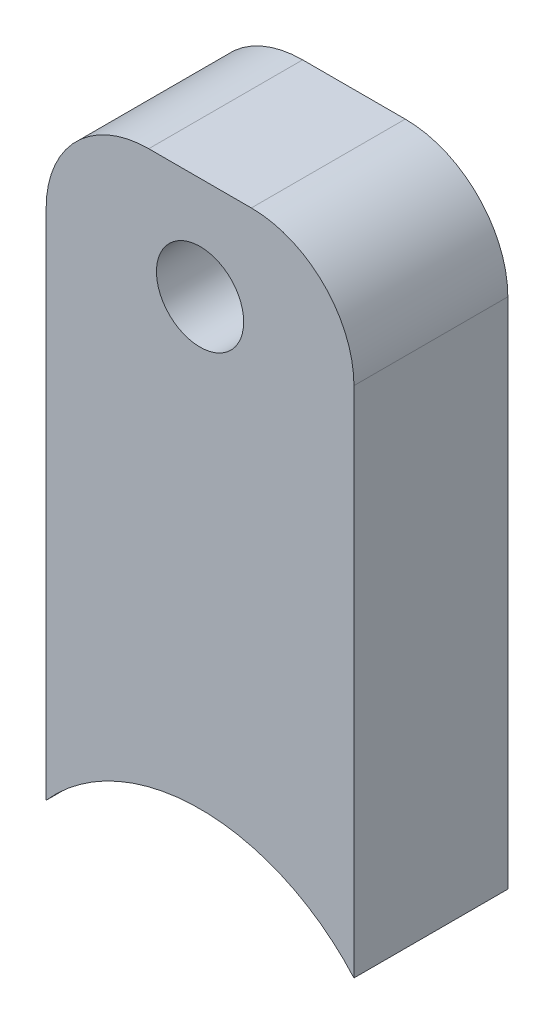
SolidWorks part; units mm, degrees
ref_plane "Plan de face" through (0, 0, 0) normal (0, 0, 1) x (1, 0, 0)
ref_plane "Plan de dessus" through (0, 0, 0) normal (0, 1, 0) x (1, 0, 0)
ref_plane "Plan de droite" through (0, 0, 0) normal (1, 0, 0) x (0, 0, -1)
sketch "Esquisse1" plane through (0, 0, 0) normal (0, 0, 1) x (1, 0, 0)
  line L0 (0, 0) -> (0, 60)
  line L1 (0, 60) -> (30, 60)
  line L4 (30, 60) -> (30, 0)
  arc A0 (0, 0) -> (30, 0) centre (15, -13.2288) cw
  dimension "D1" = 60
  dimension "D2" = 60
extrude "Boss.-Extru.1" add sketch "Esquisse1" along normal blind 15
hole_wizard "Trou taraudé M101" positions "Esquisse3" profile "Esquisse4" tap size "M10" standard "ISO" end condition through all
sketch "Esquisse3" plane through (0, 0, 15) normal (0, 0, 1) x (1, 0, 0)
  line L0 (30, 60) -> (0, 60) construction
  line L1 (0, 60) -> (0, 0) construction
  point P0 (15, 50)
  dimension "D1" = 10
  dimension "D2" = 15
sketch "Esquisse4" plane through (15, 50, 15) normal (1, 0, 0) x (0, -1, 0)
  line L0 (0, 0) -> (0, 15)
  line L1 (0, 15) -> (4.25, 15)
  line L2 (4.25, 15) -> (4.25, 0)
  line L5 (4.25, 0) -> (0, 0)
  line L11 (0, -6.35) -> (0, 107.95) construction
  dimension "Diamètre du trou pour taraudage jusqu'au prochain" = 8.5
  dimension "Profondeur du trou pour taraudage jusqu'au prochain" = 15
cosmetic thread "Filetage de perçage1"
fillet "Congé1" radius 10 2 edges at (0, 60, 7.5) (30, 60, 7.5)
